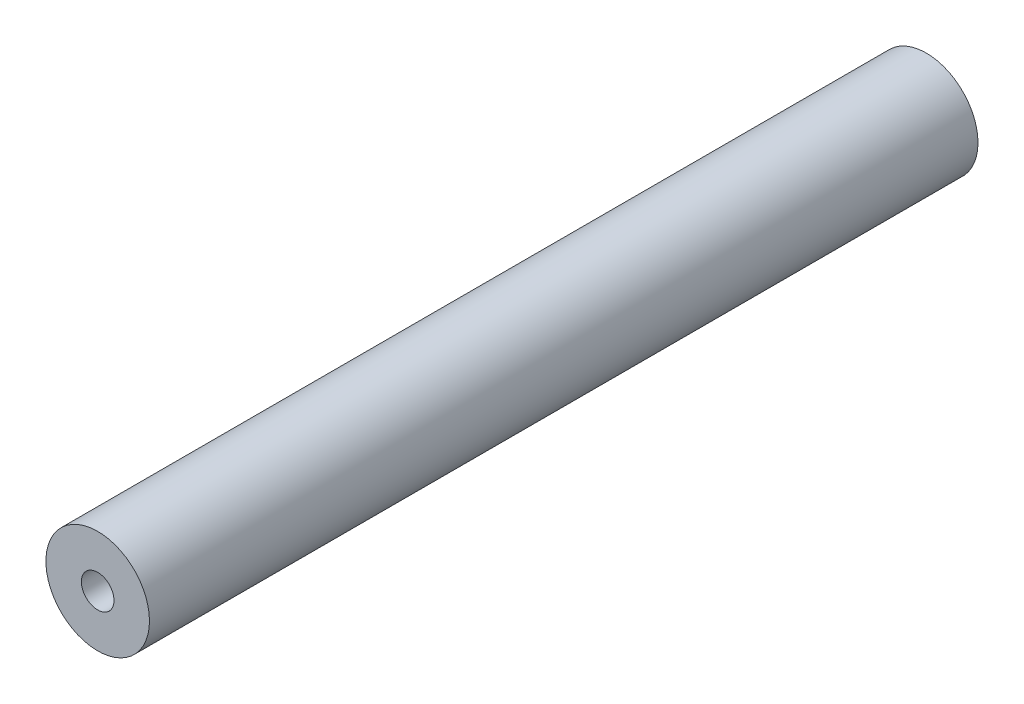
SolidWorks part; units mm, degrees
ref_plane "Front Plane" through (0, 0, 0) normal (0, 0, 1) x (1, 0, 0)
ref_plane "Top Plane" through (0, 0, 0) normal (0, 1, 0) x (1, 0, 0)
ref_plane "Right Plane" through (0, 0, 0) normal (1, 0, 0) x (0, 0, -1)
sketch "Sketch1" plane through (0, 0, 0) normal (0, 0, 1) x (1, 0, 0)
  circle A0 centre (0, 0) radius 6.35
  dimension "D1" = 12.7
extrude "Boss-Extrude1" add sketch "Sketch1" along normal blind 101.6
sketch "Sketch2" plane through (0, 0, 101.6) normal (0, 0, 1) x (1, 0, 0)
  circle A0 centre (0, 0) radius 2
  dimension "D1" = 4
extrude "Cut-Extrude1" cut sketch "Sketch2" against normal through all
